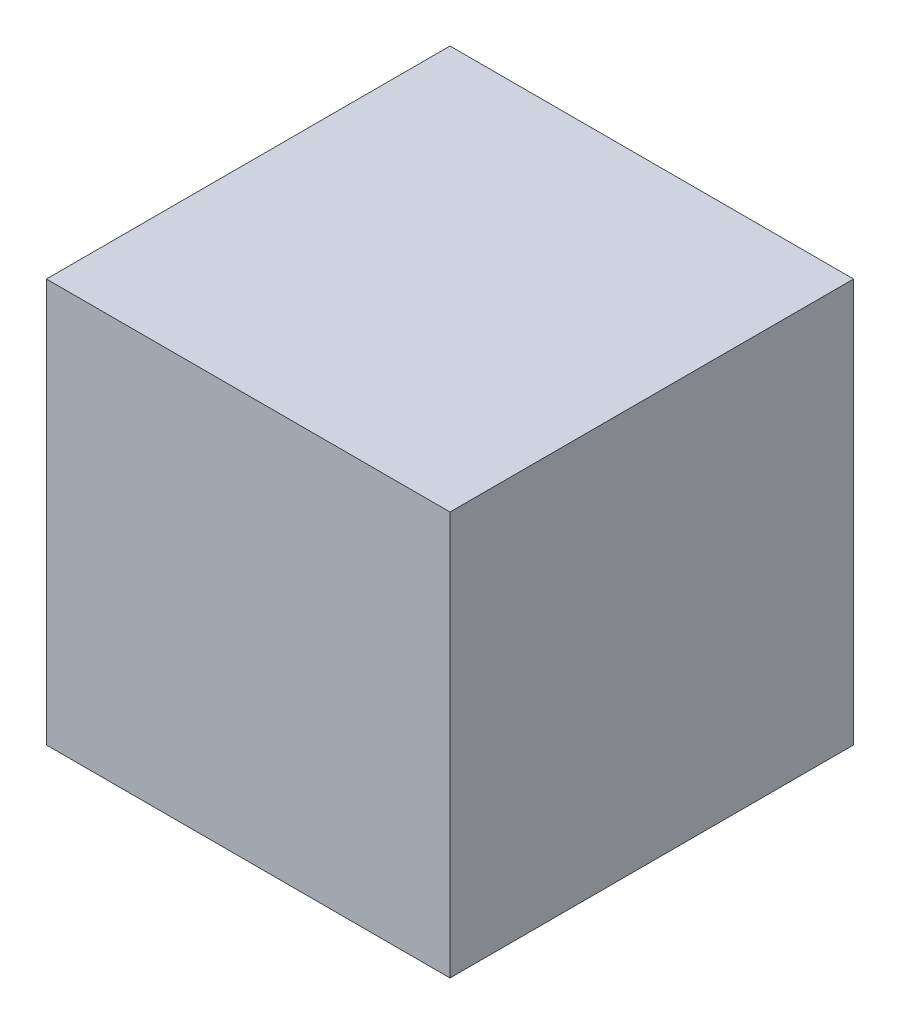
SolidWorks part; units mm, degrees
ref_plane "Front" through (0, 0, 0) normal (0, 0, 1) x (1, 0, 0)
ref_plane "Top" through (0, 0, 0) normal (0, 1, 0) x (1, 0, 0)
ref_plane "Right" through (0, 0, 0) normal (1, 0, 0) x (0, 0, -1)
sketch "Sketch1" plane through (0, 0, 0) normal (0, 1, 0) x (1, 0, 0)
  line L1 (12.7, -12.7) -> (-12.7, -12.7)
  line L2 (12.7, -12.7) -> (12.7, 12.7)
  line L3 (12.7, 12.7) -> (-12.7, 12.7)
  line L4 (-12.7, -12.7) -> (-12.7, 12.7)
  line L5 (12.7, -12.7) -> (-12.7, 12.7) construction
  line L6 (12.7, 12.7) -> (-12.7, -12.7) construction
  point P0 (0, 0)
  dimension "D1" = 25.4
  dimension "D2" = 25.4
extrude "Boss-Extrude1" add sketch "Sketch1" along normal blind 25.4
